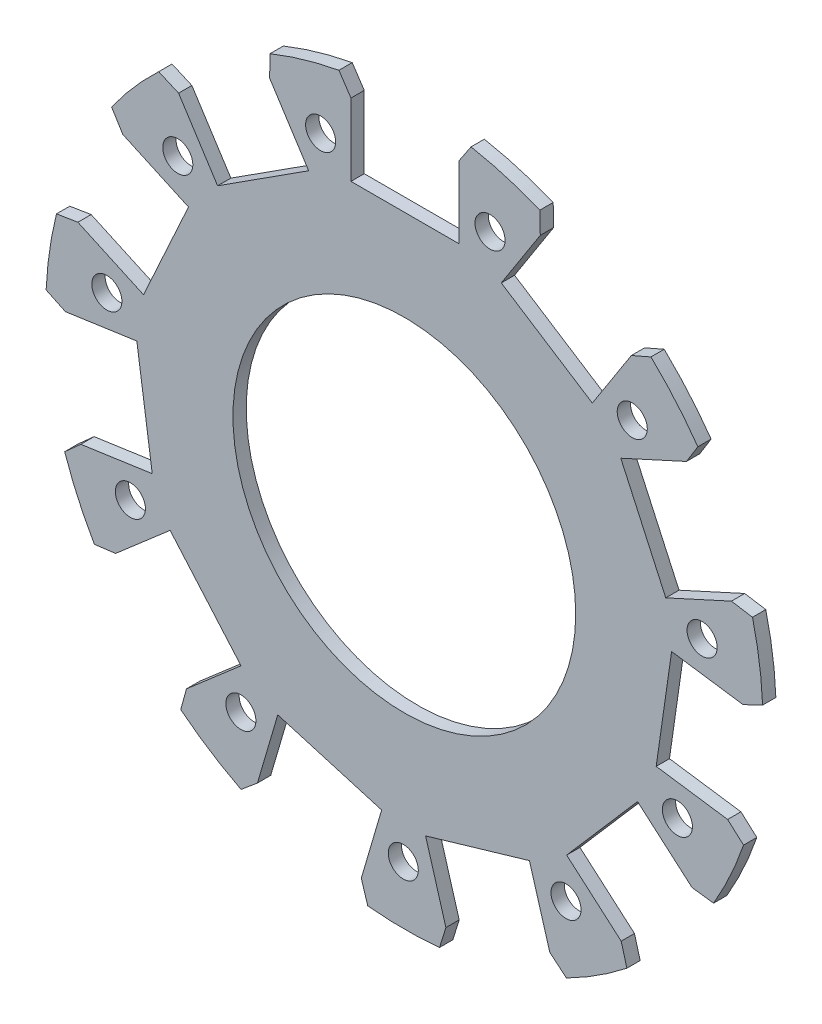
SolidWorks part; units mm, degrees
material "1060 Alloy"
ref_plane "Front Plane" through (0, 0, 0) normal (0, 0, 1) x (1, 0, 0)
ref_plane "Top Plane" through (0, 0, 0) normal (0, 1, 0) x (1, 0, 0)
ref_plane "Right Plane" through (0, 0, 0) normal (1, 0, 0) x (0, 0, -1)
sketch "Sketch1" plane through (0, 0, 0) normal (0, 0, 1) x (1, 0, 0)
  circle A0 centre (0, 0) radius 59.625
  circle A1 centre (0, 0) radius 28.5
  dimension "D1" = 57
  dimension "D2" = 119.25
extrude "Boss-Extrude1" add sketch "Sketch1" along normal blind 2.21
sketch "Sketch2" plane through (0, 0, 2.21) normal (0, 0, 1) x (1, 0, 0)
  line L0 (-8.8743, 55.625) -> (-10.8743, 58.625)
  line L1 (9.1257, 43.625) -> (-8.8743, 43.625)
  line L2 (9.1257, 43.625) -> (9.1257, 55.625)
  line L3 (9.1257, 59.625) -> (-8.8743, 59.625)
  line L4 (-8.8743, 43.625) -> (-8.8743, 55.625)
  line L5 (9.1257, 43.625) -> (-8.8743, 59.625) construction
  line L6 (9.1257, 59.625) -> (-8.8743, 43.625) construction
  line L7 (-10.8743, 58.625) -> (-8.8743, 59.625)
  line L8 (0.1257, 59.625) -> (0.1257, 43.625) construction
  line L9 (11.1257, 58.625) -> (9.1257, 59.625)
  line L10 (9.1257, 55.625) -> (11.1257, 58.625)
  line L11 (22.6076, 51.5925) -> (22.547, 55.1976)
  line L12 (31.2625, 31.7659) -> (16.1199, 41.4975)
  line L13 (31.2625, 31.7659) -> (37.7502, 41.861)
  line L14 (39.9128, 45.226) -> (24.7702, 54.9575)
  line L15 (16.1199, 41.4975) -> (22.6076, 51.5925)
  line L16 (22.547, 55.1976) -> (24.7702, 54.9575)
  line L17 (41.0546, 43.3035) -> (39.9128, 45.226)
  line L18 (37.7502, 41.861) -> (41.0546, 43.3035)
  line L19 (31.2625, 31.7659) -> (24.7702, 54.9575) construction
  line L20 (39.9128, 45.226) -> (16.1199, 41.4975) construction
  line L21 (32.3415, 50.0918) -> (23.6912, 36.6317) construction
  line L22 (46.9118, 31.1798) -> (48.8098, 34.2453)
  line L23 (43.4737, 9.8214) -> (35.9962, 26.1948)
  line L24 (43.4737, 9.8214) -> (54.3892, 14.8064)
  line L25 (58.0278, 16.4681) -> (50.5503, 32.8415)
  line L26 (35.9962, 26.1948) -> (46.9118, 31.1798)
  line L27 (48.8098, 34.2453) -> (50.5503, 32.8415)
  line L28 (57.949, 14.2334) -> (58.0278, 16.4681)
  line L29 (54.3892, 14.8064) -> (57.949, 14.2334)
  line L30 (43.4737, 9.8214) -> (50.5503, 32.8415) construction
  line L31 (58.0278, 16.4681) -> (35.9962, 26.1948) construction
  line L32 (54.289, 24.6548) -> (39.7349, 18.0081) construction
  line L33 (56.3218, 0.8677) -> (59.5759, 2.4204)
  line L34 (41.8822, -15.2413) -> (44.4439, 2.5755)
  line L35 (41.8822, -15.2413) -> (53.7601, -16.9491)
  line L36 (57.7194, -17.5184) -> (60.281, 0.2984)
  line L37 (44.4439, 2.5755) -> (56.3218, 0.8677)
  line L38 (59.5759, 2.4204) -> (60.281, 0.2984)
  line L39 (56.4449, -19.3557) -> (57.7194, -17.5184)
  line L40 (53.7601, -16.9491) -> (56.4449, -19.3557)
  line L41 (41.8822, -15.2413) -> (60.281, 0.2984) construction
  line L42 (57.7194, -17.5184) -> (44.4439, 2.5755) construction
  line L43 (59.0002, -8.61) -> (43.1631, -6.3329) construction
  line L44 (47.85, -29.7199) -> (51.427, -30.173)
  line L45 (26.9935, -35.4651) -> (38.781, -21.8616)
  line L46 (26.9935, -35.4651) -> (36.0625, -43.3234)
  line L47 (39.0855, -45.9428) -> (50.873, -32.3393)
  line L48 (38.781, -21.8616) -> (47.85, -29.7199)
  line L49 (51.427, -30.173) -> (50.873, -32.3393)
  line L50 (37.02, -46.7995) -> (39.0855, -45.9428)
  line L51 (36.0625, -43.3234) -> (37.02, -46.7995)
  line L52 (26.9935, -35.4651) -> (50.873, -32.3393) construction
  line L53 (39.0855, -45.9428) -> (38.781, -21.8616) construction
  line L54 (44.9792, -39.1411) -> (32.8872, -28.6633) construction
  line L55 (24.1862, -50.8716) -> (26.9504, -53.1866)
  line L56 (3.5345, -44.4289) -> (20.8054, -39.3577)
  line L57 (3.5345, -44.4289) -> (6.9153, -55.9428)
  line L58 (8.0422, -59.7808) -> (25.3131, -54.7096)
  line L59 (20.8054, -39.3577) -> (24.1862, -50.8716)
  line L60 (26.9504, -53.1866) -> (25.3131, -54.7096)
  line L61 (5.8415, -59.3848) -> (8.0422, -59.7808)
  line L62 (6.9153, -55.9428) -> (5.8415, -59.3848)
  line L63 (3.5345, -44.4289) -> (25.3131, -54.7096) construction
  line L64 (8.0422, -59.7808) -> (20.8054, -39.3577) construction
  line L65 (16.6777, -57.2452) -> (12.17, -41.8933) construction
  line L66 (-7.1566, -55.872) -> (-6.0828, -59.3139)
  line L67 (-21.0466, -39.2869) -> (-3.7758, -44.3581)
  line L68 (-21.0466, -39.2869) -> (-24.4274, -50.8008)
  line L69 (-25.5544, -54.6388) -> (-8.2835, -59.7099)
  line L70 (-3.7758, -44.3581) -> (-7.1566, -55.872)
  line L71 (-6.0828, -59.3139) -> (-8.2835, -59.7099)
  line L72 (-27.1916, -53.1158) -> (-25.5544, -54.6388)
  line L73 (-24.4274, -50.8008) -> (-27.1916, -53.1158)
  line L74 (-21.0466, -39.2869) -> (-8.2835, -59.7099) construction
  line L75 (-25.5544, -54.6388) -> (-3.7758, -44.3581) construction
  line L76 (-16.9189, -57.1743) -> (-12.4112, -41.8225) construction
  line L77 (-36.2272, -43.1334) -> (-37.1847, -46.6094)
  line L78 (-38.9456, -21.6715) -> (-27.1582, -35.275)
  line L79 (-38.9456, -21.6715) -> (-48.0146, -29.5299)
  line L80 (-51.0376, -32.1493) -> (-39.2501, -45.7528)
  line L81 (-27.1582, -35.275) -> (-36.2272, -43.1334)
  line L82 (-37.1847, -46.6094) -> (-39.2501, -45.7528)
  line L83 (-51.5916, -29.983) -> (-51.0376, -32.1493)
  line L84 (-48.0146, -29.5299) -> (-51.5916, -29.983)
  line L85 (-38.9456, -21.6715) -> (-39.2501, -45.7528) construction
  line L86 (-51.0376, -32.1493) -> (-27.1582, -35.275) construction
  line L87 (-45.1439, -38.9511) -> (-33.0519, -28.4733) construction
  line L88 (-53.7959, -16.7002) -> (-56.4807, -19.1068)
  line L89 (-44.4797, 2.8243) -> (-41.918, -14.9924)
  line L90 (-44.4797, 2.8243) -> (-56.3575, 1.1166)
  line L91 (-60.3168, 0.5473) -> (-57.7552, -17.2695)
  line L92 (-41.918, -14.9924) -> (-53.7959, -16.7002)
  line L93 (-56.4807, -19.1068) -> (-57.7552, -17.2695)
  line L94 (-59.6116, 2.6693) -> (-60.3168, 0.5473)
  line L95 (-56.3575, 1.1166) -> (-59.6116, 2.6693)
  line L96 (-44.4797, 2.8243) -> (-57.7552, -17.2695) construction
  line L97 (-60.3168, 0.5473) -> (-41.918, -14.9924) construction
  line L98 (-59.036, -8.3611) -> (-43.1989, -6.084) construction
  line L99 (-54.2848, 15.0351) -> (-57.8445, 14.4621)
  line L100 (-35.8917, 26.4235) -> (-43.3692, 10.0501)
  line L101 (-35.8917, 26.4235) -> (-46.8073, 31.4085)
  line L102 (-50.4458, 33.0702) -> (-57.9233, 16.6968)
  line L103 (-43.3692, 10.0501) -> (-54.2848, 15.0351)
  line L104 (-57.8445, 14.4621) -> (-57.9233, 16.6968)
  line L105 (-48.7054, 34.474) -> (-50.4458, 33.0702)
  line L106 (-46.8073, 31.4085) -> (-48.7054, 34.474)
  line L107 (-35.8917, 26.4235) -> (-57.9233, 16.6968) construction
  line L108 (-50.4458, 33.0702) -> (-43.3692, 10.0501) construction
  line L109 (-54.1846, 24.8835) -> (-39.6305, 18.2368) construction
  line L110 (-37.5387, 41.9969) -> (-40.8431, 43.4394)
  line L111 (-15.9084, 41.6334) -> (-31.051, 31.9019)
  line L112 (-15.9084, 41.6334) -> (-22.3961, 51.7285)
  line L113 (-24.5587, 55.0935) -> (-39.7012, 45.3619)
  line L114 (-31.051, 31.9019) -> (-37.5387, 41.9969)
  line L115 (-40.8431, 43.4394) -> (-39.7012, 45.3619)
  line L116 (-22.3355, 55.3335) -> (-24.5587, 55.0935)
  line L117 (-22.3961, 51.7285) -> (-22.3355, 55.3335)
  line L118 (-15.9084, 41.6334) -> (-39.7012, 45.3619) construction
  line L119 (-24.5587, 55.0935) -> (-31.051, 31.9019) construction
  line L120 (-32.1299, 50.2277) -> (-23.4797, 36.7677) construction
  circle A0 centre (0, 0) radius 59.625 construction
  point P0 (0.1257, 51.625)
  point P14 (28.0163, 43.3617)
  point P27 (47.012, 21.3314)
  point P38 (51.0816, -7.4714)
  point P49 (38.9332, -33.9022)
  point P60 (14.4238, -49.5692)
  point P71 (-14.6651, -49.4984)
  point P82 (-39.0979, -33.7122)
  point P93 (-51.1174, -7.2226)
  point P104 (-46.9075, 21.5602)
  point P115 (-27.8048, 43.4977)
  point P126 (0, 0)
  dimension "D4" = 2
sketch "Sketch3" plane through (0, 0, 0) normal (0, 0, -1) x (-1, 0, 0)
  circle A0 centre (0, 0) radius 50
  circle A1 centre (-13.3875, 48.1744) radius 2.5
  dimension "D1" = 100
  dimension "D2" = 5
extrude "Cut-Extrude2" cut sketch "Sketch2" against normal blind 2.21
sketch "Sketch6" plane through (0, 0, 2.21) normal (0, 0, 1) x (1, 0, 0)
  line L0 (-15.9084, 41.6334) -> (-8.8743, 43.625)
  line L1 (-13.9187, 48.0236) -> (-12.3913, 42.6292)
  circle A1 centre (-13.9187, 48.0236) radius 2.5
  circle A2 centre (14.2544, 47.9251) radius 2.5
  circle A3 centre (37.9018, 32.6106) radius 2.5
  circle A4 centre (49.5157, 6.9425) radius 2.5
  circle A5 centre (45.4086, -20.9298) radius 2.5
  circle A6 centre (26.8847, -42.157) radius 2.5
  circle A7 centre (-0.175, -49.9997) radius 2.5
  circle A8 centre (-27.1791, -41.9678) radius 2.5
  circle A9 centre (-45.554, -20.6115) radius 2.5
  circle A10 centre (-49.4659, 7.2889) radius 2.5
  circle A11 centre (-37.6727, 32.8751) radius 2.5
  point P33 (0, 0)
  dimension "D2" = 5
  dimension "D3" = 90
  dimension "D4" = 11
extrude "Cut-Extrude4" cut sketch "Sketch6" against normal blind 2.21
